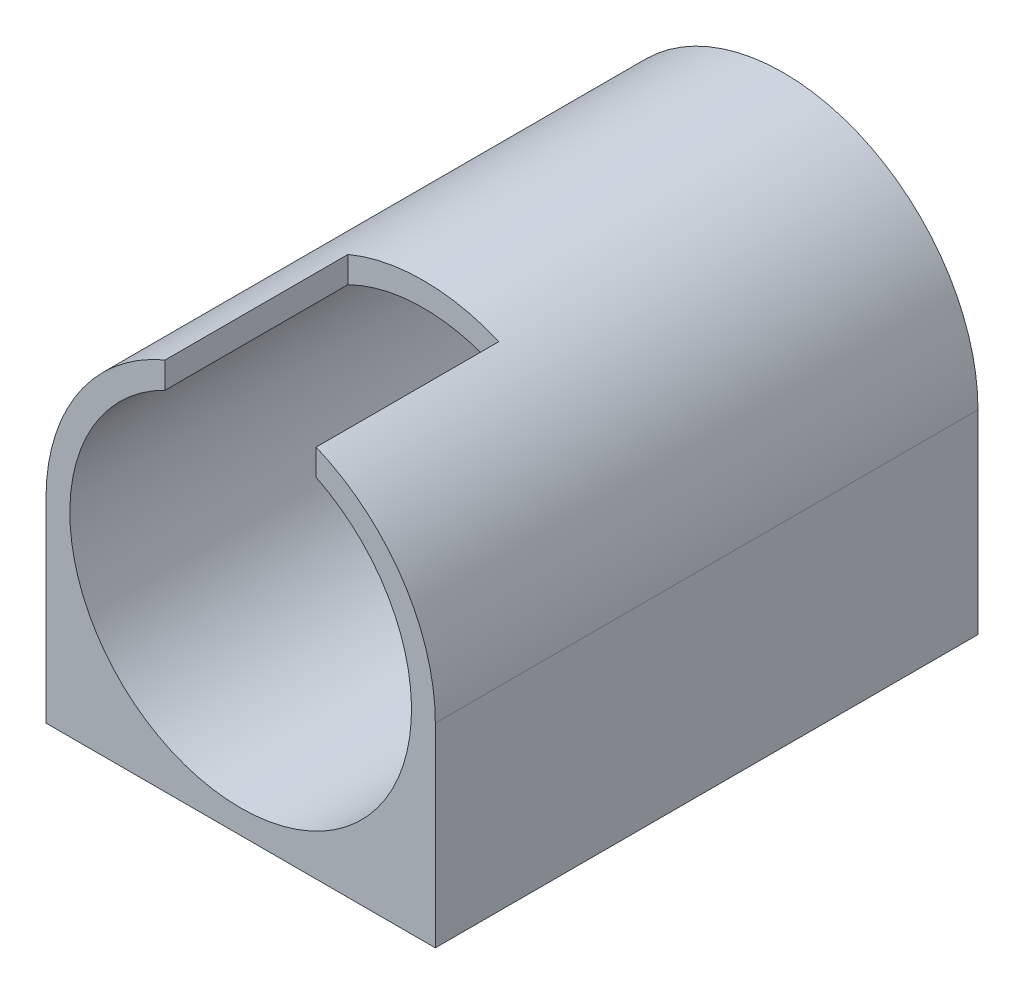
SolidWorks part; units mm, degrees
ref_plane "Plan de face" through (0, 0, 0) normal (0, 0, 1) x (1, 0, 0)
ref_plane "Plan de dessus" through (0, 0, 0) normal (0, 1, 0) x (1, 0, 0)
ref_plane "Plan de droite" through (0, 0, 0) normal (1, 0, 0) x (0, 0, -1)
sketch "Esquisse1" plane through (0, 0, 0) normal (0, 0, 1) x (1, 0, 0)
  line L1 (-24.5, -24.5) -> (24.5, -24.5)
  line L2 (-24.5, -24.5) -> (-24.5, 0)
  line L4 (24.5, -24.5) -> (24.5, 0)
  line L5 (-24.5, -24.5) -> (17.3241, 17.3241) construction
  line L6 (-17.3241, 17.3241) -> (24.5, -24.5) construction
  circle A0 centre (0, 0) radius 24.5
  circle A1 centre (0, 0) radius 21.5
  dimension "D1" = 49
  dimension "D5" = 43
  dimension "D2" = 24.5
  dimension "D3" = 49
  dimension "D4" = 24.5
extrude "Boss.-Extru.1" add sketch "Esquisse1" along normal blind 65.3 contours A0 A1 | A0 L2 L1 | A0 L1 L4
sketch "Esquisse2" plane through (0, 0, 0) normal (0, 0, -1) x (-1, 0, 0)
  line L2 (-24.5, 0) -> (-24.5, -24.5)
  line L3 (-24.5, -24.5) -> (24.5, -24.5)
  line L4 (24.5, 0) -> (24.5, -24.5)
  line L5 (-17.3241, 17.3241) -> (24.5, -24.5) construction
  line L6 (-24.5, -24.5) -> (17.3241, 17.3241) construction
  circle A0 centre (0, 0) radius 24.5
  circle A1 centre (0, 0) radius 14.5
  circle M1 centre (0, 0) radius 21.5
  arc M2 (24.5, 0) -> (-24.5, 0) centre (0, 0) ccw
  line M3 (-24.5, 0) -> (-24.5, -24.5)
  line M4 (-24.5, -24.5) -> (24.5, -24.5)
  line M5 (24.5, -24.5) -> (24.5, 0)
  dimension "D1" = 29
extrude "Boss.-Extru.2" add sketch "Esquisse2" along normal blind 3 contours A1 M1 | A0 M2 M1 | A0 M3 M4 | A0 L3 M5
sketch "Esquisse3" plane through (0, 0, -3) normal (0, 0, -1) x (-1, 0, 0)
  line L0 (-17.5, 0) -> (17.5, 0) construction
  line L1 (0, 17.5) -> (0, -17.5) construction
  circle A0 centre (-17.5, 0) radius 1.65
  circle A1 centre (17.5, 0) radius 1.65
  circle A2 centre (0, 17.5) radius 1.65
  circle A3 centre (0, -17.5) radius 1.65
  point P3 (0, 0)
  point P8 (0, 0)
  dimension "D2" = 3.3
  dimension "D3" = 3.3
  dimension "D5" = 3.3
  dimension "D6" = 3.3
  dimension "D1" = 35
  dimension "D4" = 35
extrude "Enlèv. mat.-Extru.1" cut sketch "Esquisse3" against normal blind 3
sketch "Esquisse4" plane through (0, 0, 65.3) normal (0, 0, 1) x (1, 0, 0)
  line L0 (-9.5, 19.2873) -> (9.5, 19.2873) construction
  line L1 (-9.5, 19.2873) -> (-9.5, 25.0257) construction
  line L2 (-9.5, 25.0257) -> (9.5, 25.0257) construction
  line L3 (9.5, 25.0257) -> (9.5, 19.2873) construction
  line L4 (-9.5, 25.0257) -> (9.5, 25.0257)
  line L5 (9.5, 25.0257) -> (9.5, 19.2873)
  line L6 (9.5, 19.2873) -> (-9.5, 19.2873)
  line L7 (-9.5, 19.2873) -> (-9.5, 25.0257)
  circle A0 centre (0, 0) radius 21.5 construction
  dimension "D1" = 19
extrude "Enlèv. mat.-Extru.2" cut sketch "Esquisse4" against normal blind 23
sketch "Esquisse5" plane through (-24.5, 0, 0) normal (-1, 0, 0) x (0, 0, 1)
  line L0 (-3, -24.5) -> (-3, -21.5)
  line L1 (-3, -24.5) -> (-3, 0) construction
  line L2 (-3, -21.5) -> (65.3, -21.5)
  line L3 (65.3, -24.5) -> (65.3, 0) construction
  line L4 (65.3, -21.5) -> (65.3, -24.5)
  line L5 (65.3, -24.5) -> (-3, -24.5)
  dimension "D1" = 3
extrude "Boss.-Extru.3" add sketch "Esquisse5" along normal blind 17
sketch "Esquisse6" plane through (24.5, 0, 0) normal (1, 0, 0) x (0, 0, -1)
  line L0 (-65.3, -24.5) -> (-65.3, -21.5)
  line L1 (-65.3, -21.5) -> (3, -21.5)
  line L2 (3, -21.5) -> (3, -24.5)
  line L3 (3, -24.5) -> (-65.3, -24.5)
extrude "Boss.-Extru.4" add sketch "Esquisse6" along normal blind 17
sketch "Esquisse7" plane through (0, -21.5, 0) normal (0, 1, 0) x (1, 0, 0)
  line L0 (-24.5, -7) -> (-41.5, -7) construction
  line L1 (-24.5, -65.3) -> (-24.5, 3) construction
  line L2 (-41.5, -65.3) -> (-41.5, 3) construction
  line L3 (-41.5, 3) -> (-24.5, 3) construction
  line L4 (-24.5, -55.3) -> (-41.5, -55.3) construction
  line L5 (-41.5, -65.3) -> (-24.5, -65.3) construction
  circle A0 centre (-33, -7) radius 2
  circle A1 centre (-33, -55.3) radius 2
  dimension "D3" = 4
  dimension "D4" = 4
  dimension "D1" = 10
  dimension "D2" = 10
sketch "Esquisse9" plane through (0, -21.5, 0) normal (0, 1, 0) x (1, 0, 0)
  line L0 (24.5, -7) -> (41.5, -7) construction
  line L1 (24.5, 3) -> (24.5, -65.3) construction
  line L2 (41.5, 3) -> (41.5, -65.3) construction
  line L3 (24.5, -55.3) -> (41.5, -55.3) construction
  line L4 (41.5, 3) -> (24.5, 3) construction
  line L5 (41.5, -65.3) -> (24.5, -65.3) construction
  circle A0 centre (33, -7) radius 2
  circle A1 centre (33, -55.3) radius 2
  dimension "D3" = 4
  dimension "D4" = 4
  dimension "D1" = 10
  dimension "D2" = 10
extrude "Enlèv. mat.-Extru.3" cut sketch "Esquisse7" against normal blind 10
extrude "Enlèv. mat.-Extru.4" cut sketch "Esquisse9" against normal blind 10
sketch "Esquisse10" plane through (0, -24.5, 0) normal (0, -1, 0) x (1, 0, 0)
  line L0 (-33, 55.3) -> (33, 55.3) construction
  line L1 (0, 63.6573) -> (0, 46.9427) construction
  line L2 (-24.5, 65.3) -> (-24.5, -3) construction
  line L3 (-33, 55.3) -> (-33, 7) construction
  line L4 (-33, 31.15) -> (33, 31.15) construction
  circle A0 centre (-19.5, 55.3) radius 3.5
  circle A1 centre (19.5, 55.3) radius 3.5
  circle A2 centre (19.5, 7) radius 3.5
  circle A3 centre (-19.5, 7) radius 3.5
  point P8 (0, 55.3)
  dimension "D1" = 7
  dimension "D2" = 5
extrude "Enlèv. mat.-Extru.5" cut sketch "Esquisse10" against normal blind 1
sketch "Esquisse11" plane through (0, -24.5, 0) normal (0, -1, 0) x (1, 0, 0)
  line L0 (-33, 55.3) -> (33, 55.3) construction
  line L1 (0, 61.5941) -> (0, 49.0059) construction
  line L2 (-33, 55.3) -> (-33, 7) construction
  line L3 (-33, 31.15) -> (33, 31.15) construction
  circle A0 centre (-19.5, 55.3) radius 2.75
  circle A1 centre (19.5, 55.3) radius 2.75
  circle A2 centre (19.5, 7) radius 2.75
  circle A3 centre (-19.5, 7) radius 2.75
  point P8 (0, 55.3)
  dimension "D1" = 5.5
extrude "Enlèv. mat.-Extru.6" cut sketch "Esquisse11" against normal blind 8
sketch "Esquisse12" plane through (0, 0, -3) normal (0, 0, -1) x (-1, 0, 0)
  line L1 (-24.5, -21.5) -> (-41.5, -21.5)
  line L2 (-24.5, -21.5) -> (-24.5, -24.5)
  line L3 (-24.5, -24.5) -> (-41.5, -24.5)
  line L4 (-41.5, -21.5) -> (-41.5, -24.5)
  line L5 (24.5, -21.5) -> (41.5, -21.5)
  line L6 (24.5, -21.5) -> (24.5, -24.5)
  line L7 (24.5, -24.5) -> (41.5, -24.5)
  line L8 (41.5, -21.5) -> (41.5, -24.5)
extrude "Enlèv. mat.-Extru.7" cut sketch "Esquisse12" against normal blind 74
